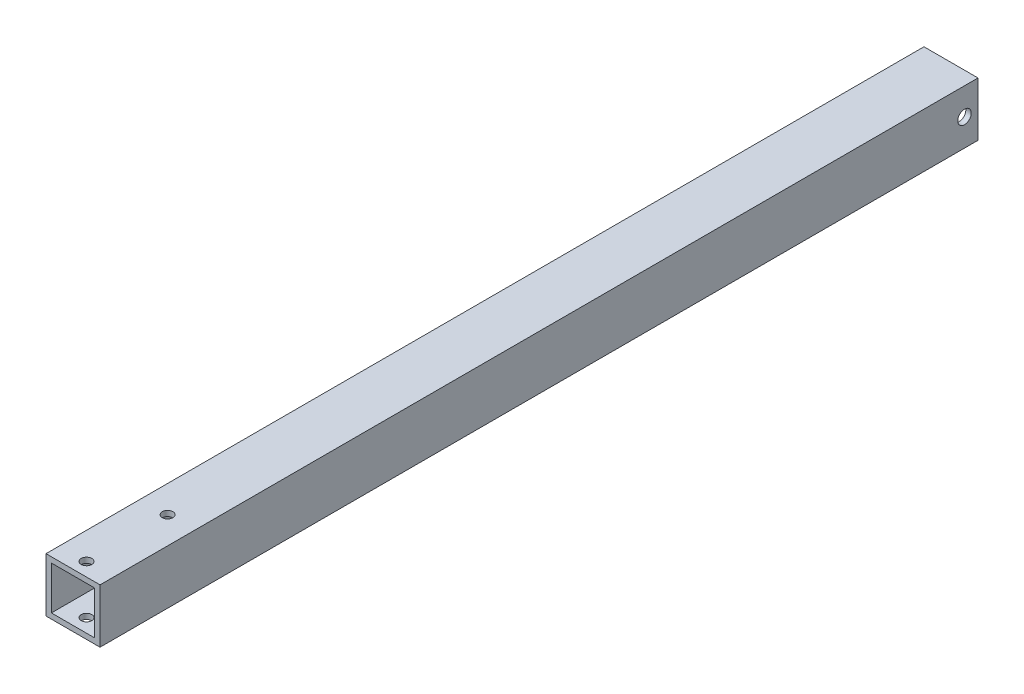
SolidWorks part; units mm, degrees
material "6061-T6 (SS)"
ref_plane "Front Plane" through (0, 0, 0) normal (0, 0, 1) x (1, 0, 0)
ref_plane "Top Plane" through (0, 0, 0) normal (0, 1, 0) x (1, 0, 0)
ref_plane "Right Plane" through (0, 0, 0) normal (1, 0, 0) x (0, 0, -1)
sketch "Sketch1" plane through (0, 0, 0) normal (0, 0, 1) x (1, 0, 0)
  line L1 (-12.7, 12.7) -> (12.7, 12.7)
  line L2 (-12.7, 12.7) -> (-12.7, -12.7)
  line L3 (-12.7, -12.7) -> (12.7, -12.7)
  line L4 (12.7, 12.7) -> (12.7, -12.7)
  line L5 (-12.7, 12.7) -> (12.7, -12.7) construction
  line L6 (-12.7, -12.7) -> (12.7, 12.7) construction
  point P0 (0, 0)
  dimension "D1" = 25.4
extrude "Extrude-Thin1" add sketch "Sketch1" along normal blind 412.75 thin
sketch "Sketch2" plane through (0, 12.7, 0) normal (0, 1, 0) x (1, 0, 0)
  line L0 (0, -412.75) -> (0, -368.3) construction
  line L1 (12.7, -412.75) -> (-12.7, -412.75) construction
  circle A0 centre (0, -406.4) radius 2.4892
  circle A1 centre (0, -368.3) radius 2.4892
  dimension "D1" = 4.9784
  dimension "D2" = 6.35
  dimension "D3" = 38.1
extrude "Cut-Extrude1" cut sketch "Sketch2" against normal through all
sketch "Sketch3" plane through (12.7, 0, 0) normal (1, 0, 0) x (0, 0, -1)
  line L0 (0, -12.7) -> (0, 12.7) construction
  line L1 (-412.75, 12.7) -> (0, 12.7) construction
  circle A0 centre (-6.35, 0) radius 3.175
  dimension "D1" = 6.35
  dimension "D2" = 6.35
  dimension "D3" = 12.7
extrude "Cut-Extrude2" cut sketch "Sketch3" against normal through all
equation "\"Thick\"= \"in\""
